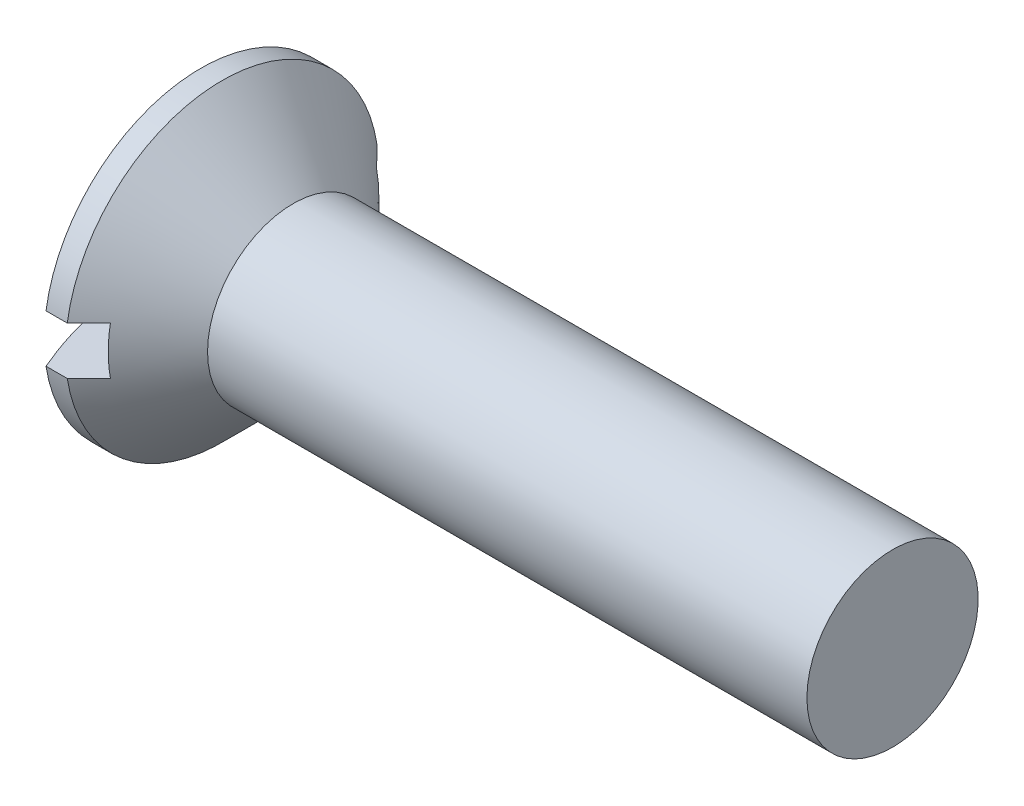
SolidWorks part; units mm, degrees
revolve "Base-Revolve" add sketch "BodySke" angle 360 about L4
sketch "BodySke" plane through (0, 0, 0) normal (0, 0, 1) x (1, 0, 0)
  line L0 (0, 0) -> (42.2988, 0)
  line L1 (42.2988, 0) -> (42.2988, 5)
  line L2 (42.2988, 5) -> (7.2988, 5)
  line L3 (7.2988, 5) -> (-0.5742, 12.873) construction
  line L4 (-15.875, 0) -> (82.55, 0) construction
  line L5 (7.2988, -5) -> (-0.5742, -12.873) construction
  line L6 (8.7988, 8.175) -> (8.7988, -7.7) construction
  line L7 (2.2988, 5.2375) -> (2.2988, -10.6375) construction
  line L8 (7.2988, 5) -> (3.1488, 9.15)
  line L9 (3.1488, 9.15) -> (1.9074, 9.15)
  arc A0 (0, 0) -> (1.9074, 9.15) centre (22.9, 0) cw
  arc A1 (2.2988, 10) -> (0, 0) centre (22.9, 0) ccw construction
  dimension "Head_ang" = 90
cosmetic thread "ThreadCosmetic" [suppressed] parameters "Thread_length"=16.5, "Thread_minor"=8.344
ref_plane "Plane1" through (0, 0, 0) normal (0, 0, 1) x (1, 0, 0)
ref_plane "Plane2" through (0, 0, 0) normal (0, 1, 0) x (1, 0, 0)
ref_plane "Plane3" through (0, 0, 0) normal (1, 0, 0) x (0, 0, -1)
other "Configuration Table"
sketch "Sketch2" plane through (0, 0, 0) normal (1, 0, 0) x (0, 0, -1)
  line L0 (9.15, -1.4) -> (-9.15, -1.4)
  line L1 (9.15, -1.4) -> (9.15, 1.4)
  line L2 (-9.15, 1.4) -> (9.15, 1.4)
  line L3 (-9.15, 1.4) -> (-9.15, -1.4)
  dimension "D1" = 9.3
  dimension "D3" = 4.65
  dimension "D4" = 0.75
extrude "Slot" cut sketch "Sketch2" along normal blind 4.4
sketch "Sketch3" plane through (0, 0, 0) normal (1, 0, 0) x (0, 0, -1)
  line L0 (1.085, -5.62) -> (-1.085, -5.62)
  line L1 (1.085, -5.62) -> (1.085, 5.62)
  line L2 (-1.085, 5.62) -> (1.085, 5.62)
  line L3 (-1.085, 5.62) -> (-1.085, -5.62)
  dimension "D1" = 0.55
  dimension "D2" = 2.83
ref_plane "Plane4" through (7.15, 0, 0) normal (1, 0, 0) x (0, 0, -1)
sketch "Sketch4" plane through (7.15, 0, 0) normal (1, 0, 0) x (0, 0, -1)
  line L0 (0.5425, -0.5425) -> (-0.5425, -0.5425)
  line L1 (0.5425, -0.5425) -> (0.5425, 0.5425)
  line L2 (-0.5425, 0.5425) -> (0.5425, 0.5425)
  line L3 (-0.5425, 0.5425) -> (-0.5425, -0.5425)
  dimension "D1" = 0.55
  dimension "D2" = 0.55
  dimension "D3" = 0.275
  dimension "D4" = 0.275
loft "Cross" cut profiles "Sketch3", "Sketch4"
pattern_circular "CirPattern1" count 2 every 90 about axis through (0, 0, 0) along (1, 0, 0) of "Cross"
sketch "ThdSchSke" plane through (0, 0, 0) normal (0, 0, 1) x (1, 0, 0)
  line L0 (8.7988, -4.172) -> (8.219, -5)
  line L1 (8.7988, -4.172) -> (9.3786, -5)
  line L2 (9.3786, -5) -> (9.3786, -6.25)
  line L3 (-3.175, 0) -> (5.1513, 0) construction
  line L5 (9.3786, -6.25) -> (8.219, -6.25)
  line L6 (8.219, -6.25) -> (8.219, -5)
  line L8 (42.2988, -5) -> (42.2988, 5) construction
  dimension "Thread_minor" = 4.11
  dimension "Diameter" = 5
  dimension "Start" = 16.5
revolve "ThreadSchematic" [suppressed] cut sketch "ThdSchSke" angle 360 about L3
pattern_linear "ThdSchPat" [suppressed]
equation "\"D1@Sketch2\" = \"Head_dia@BodySke\""
equation "\"D3@Sketch2\" = \"D1@Sketch2\" / 2"
equation "\"D4@Sketch2\" = \"Slot_width@Sketch2\" / 2"
equation "\"D1@Sketch3\" = \"Cross_width@Sketch3\" / 2"
equation "\"D2@Sketch3\" = \"Cross_dia@Sketch3\" / 2"
equation "\"D1@Sketch4\" = \"Cross_width@Sketch3\"*.5"
equation "\"D2@Sketch4\" = \"D1@Sketch4\""
equation "\"D3@Sketch4\" = \"D1@Sketch4\" / 2"
equation "\"D4@Sketch4\" = \"D2@Sketch4\" / 2"
equation "\"Thread_length@ThreadCosmetic\" = ((sgn( (\"Length@BodySke\" - \"Advance@BodySke\" - \"Side_ht@BodySke\" ) - \"Thread_nom@BodySke\" )-1)*( (\"Length@BodySke\" - \"Advance@BodySke\" - \"Side_ht@BodySke\" ) - \"Thread_nom@BodySke\" ))/-2+ \"Thread_nom@BodySke\""
equation "\"Thread_minor@ThdSchSke\" = \"Thread_minor@ThreadCosmetic\""
equation "\"Diameter@ThdSchSke\" = \"Diameter@BodySke\""
equation "\"Overcut@ThdSchSke\" = \"Diameter@BodySke\" * 1.25"
equation "\"Start@ThdSchSke\" =  \"Thread_length@ThreadCosmetic\""
equation "\"Num_threads@ThdSchPat\" = int( \"Thread_length@ThreadCosmetic\" / \"Advance@BodySke\" + 0.999 )  + 1"
equation "\"Advance@ThdSchPat\" = \"Thread_length@ThreadCosmetic\" /  (\"Num_threads@ThdSchPat\" - 1) 'relax it"
